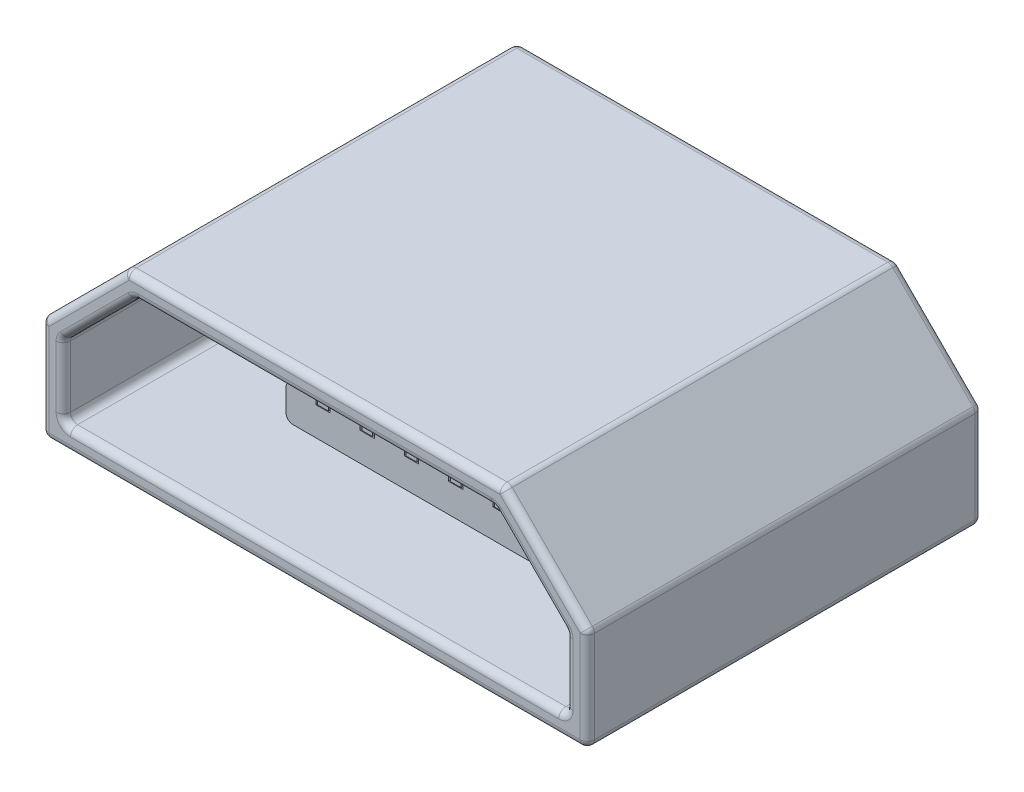
SolidWorks part; units mm, degrees
ref_plane "Front" through (0, 0, 0) normal (0, 0, 1) x (1, 0, 0)
ref_plane "Top" through (0, 0, 0) normal (0, 1, 0) x (1, 0, 0)
ref_plane "Right" through (0, 0, 0) normal (1, 0, 0) x (0, 0, -1)
sketch "Sketch1" plane through (0, 0, 0) normal (0, 0, 1) x (1, 0, 0)
  line L0 (0, 0) -> (7, 0)
  line L1 (7, 0) -> (7, 1)
  line L2 (7, 1) -> (6, 2)
  line L3 (6, 2) -> (1, 2)
  line L4 (1, 2) -> (0, 1)
  line L5 (0, 1) -> (0, 0)
  dimension "D1" = 7
  dimension "D2" = 2
  dimension "D3" = 1
extrude "Extrude-Thin1" add sketch "Sketch1" along normal blind 5.5 thin
sketch "Sketch2" plane through (0, 0, 0) normal (0, 0, -1) x (-1, 0, 0)
  line L0 (-6, 2) -> (-1, 2)
  line L1 (-1, 2) -> (0, 1)
  line L2 (0, 1) -> (0, 0)
  line L3 (0, 0) -> (-7, 0)
  line L4 (-7, 0) -> (-7, 1)
  line L5 (-7, 1) -> (-6, 2)
extrude "Boss-Extrude1" add sketch "Sketch2" against normal blind 2.5
sketch "Sketch3" plane through (0, 0, 2.5) normal (0, 0, 1) x (1, 0, 0)
  line L0 (0, 0.5) -> (1.75, 0.5) construction
  line L1 (1.75, 0.75) -> (5.25, 0.75)
  line L2 (1.75, 0.75) -> (1.75, 0.25)
  line L3 (1.75, 0.25) -> (5.25, 0.25)
  line L4 (5.25, 0.75) -> (5.25, 0.25)
  line L5 (0, 1) -> (0, 0) construction
  line L6 (5.25, 0.5) -> (7, 0.5) construction
  line L7 (7, 0) -> (7, 1) construction
  dimension "D1" = 3.5
  dimension "D2" = 0.5
extrude "Boss-Extrude2" add sketch "Sketch3" along normal blind 1.65
sketch "Sketch4" plane through (0, 0, 4.15) normal (0, 0, 1) x (1, 0, 0)
  line L0 (5.25, 0.75) -> (1.75, 0.75) construction
  line L1 (2.3667, 0.65) -> (2.1667, 0.65)
  line L2 (2.3667, 0.65) -> (2.3667, 0.75)
  line L3 (2.3667, 0.75) -> (2.1667, 0.75)
  line L4 (2.1667, 0.65) -> (2.1667, 0.75)
  line L5 (5.25, 0.75) -> (4.8333, 0.75) construction
  line L6 (2.7833, 0.75) -> (2.9833, 0.75)
  line L7 (2.7833, 0.75) -> (2.7833, 0.65)
  line L8 (2.7833, 0.65) -> (2.9833, 0.65)
  line L9 (2.9833, 0.75) -> (2.9833, 0.65)
  line L10 (3.4, 0.75) -> (3.6, 0.75)
  line L11 (3.4, 0.75) -> (3.4, 0.65)
  line L12 (3.4, 0.65) -> (3.6, 0.65)
  line L13 (3.6, 0.75) -> (3.6, 0.65)
  line L14 (4.0167, 0.75) -> (4.2167, 0.75)
  line L15 (4.0167, 0.75) -> (4.0167, 0.65)
  line L16 (4.0167, 0.65) -> (4.2167, 0.65)
  line L17 (4.2167, 0.75) -> (4.2167, 0.65)
  line L18 (4.6333, 0.75) -> (4.8333, 0.75)
  line L19 (4.6333, 0.75) -> (4.6333, 0.65)
  line L20 (4.6333, 0.65) -> (4.8333, 0.65)
  line L21 (4.8333, 0.75) -> (4.8333, 0.65)
  line L22 (4.2167, 0.75) -> (4.6333, 0.75) construction
  line L23 (3.6, 0.75) -> (4.0167, 0.75) construction
  line L24 (2.9833, 0.75) -> (3.4, 0.75) construction
  line L25 (2.3667, 0.75) -> (2.7833, 0.75) construction
  line L26 (1.75, 0.75) -> (2.1667, 0.75) construction
  dimension "D1" = 0.2
  dimension "D2" = 0.1
extrude "Cut-Extrude1" cut sketch "Sketch4" against normal up to surface (1.65 mm away) up to face at (3.5, 1, 2.5)
sketch "Sketch5" plane through (0, 0, 4.15) normal (0, 0, 1) x (1, 0, 0)
  line L0 (2.1667, 0.75) -> (1.75, 0.75) construction
  line L1 (2.1917, 0.75) -> (2.3417, 0.75)
  line L2 (2.1917, 0.75) -> (2.1917, 0.66)
  line L3 (2.1917, 0.66) -> (2.3417, 0.66)
  line L4 (2.3417, 0.75) -> (2.3417, 0.66)
  line L5 (2.1667, 0.75) -> (2.1667, 0.65) construction
  line L7 (2.8083, 0.75) -> (2.9583, 0.75)
  line L8 (2.8083, 0.75) -> (2.8083, 0.66)
  line L9 (2.8083, 0.66) -> (2.9583, 0.66)
  line L11 (2.9583, 0.75) -> (2.9583, 0.66)
  line L12 (3.425, 0.75) -> (3.575, 0.75)
  line L13 (3.425, 0.75) -> (3.425, 0.66)
  line L14 (3.425, 0.66) -> (3.575, 0.66)
  line L16 (3.575, 0.75) -> (3.575, 0.66)
  line L17 (4.0417, 0.75) -> (4.1917, 0.75)
  line L18 (4.0417, 0.75) -> (4.0417, 0.66)
  line L19 (4.0417, 0.66) -> (4.1917, 0.66)
  line L20 (4.1917, 0.75) -> (4.1917, 0.66)
  line L21 (4.6583, 0.75) -> (4.8083, 0.75)
  line L22 (4.6583, 0.75) -> (4.6583, 0.66)
  line L23 (4.6583, 0.66) -> (4.8083, 0.66)
  line L25 (4.8083, 0.75) -> (4.8083, 0.66)
  line L27 (2.1667, 0.75) -> (2.1917, 0.75) construction
  line L29 (2.7833, 0.75) -> (2.8083, 0.75) construction
  line L30 (3.4, 0.75) -> (3.425, 0.75) construction
  line L31 (4.0167, 0.75) -> (4.0417, 0.75) construction
  line L32 (4.6333, 0.75) -> (4.6583, 0.75) construction
  dimension "D1" = 0.15
  dimension "D2" = 0.025
  dimension "D3" = 0.09
extrude "Boss-Extrude4" add sketch "Sketch5" against normal up to next
fillet "Fillet1" radius 0.1 34 edges at (0, 1, 4) (7, 1, 4) (7, 0, 4) (0, 0, 4) (1, 2, 4) (6, 2, 4) (1.75, 0.25, 3.325) (1.75, 0.75, 3.325) (5.25, 0.25, 3.325) (5.25, 0.75, 3.325) (7.3, 0.4121, 0) (3.5, -0.3, 0) (-0.3, 0.4121, 0) (0.2879, 1.7121, 0) (3.5, 2.3, 0) (6.5, 1.5, 5.5) (7, 0.5, 5.5) (3.5, 0, 5.5) (0, 0.5, 5.5) (0.5, 1.5, 5.5) (3.5, 2, 5.5) (-0.3, 0.4121, 5.5) (0.2879, 1.7121, 5.5) (3.5, 2.3, 5.5) (3.5, -0.3, 5.5) (7.3, 0.4121, 5.5) (6.7121, 1.7121, 5.5) (6.1243, 2.3, 2.75) (7.3, 1.1243, 2.75) (7.3, -0.3, 2.75) (-0.3, -0.3, 2.75) (-0.3, 1.1243, 2.75) (0.8757, 2.3, 2.75) (6.7121, 1.7121, 0)
